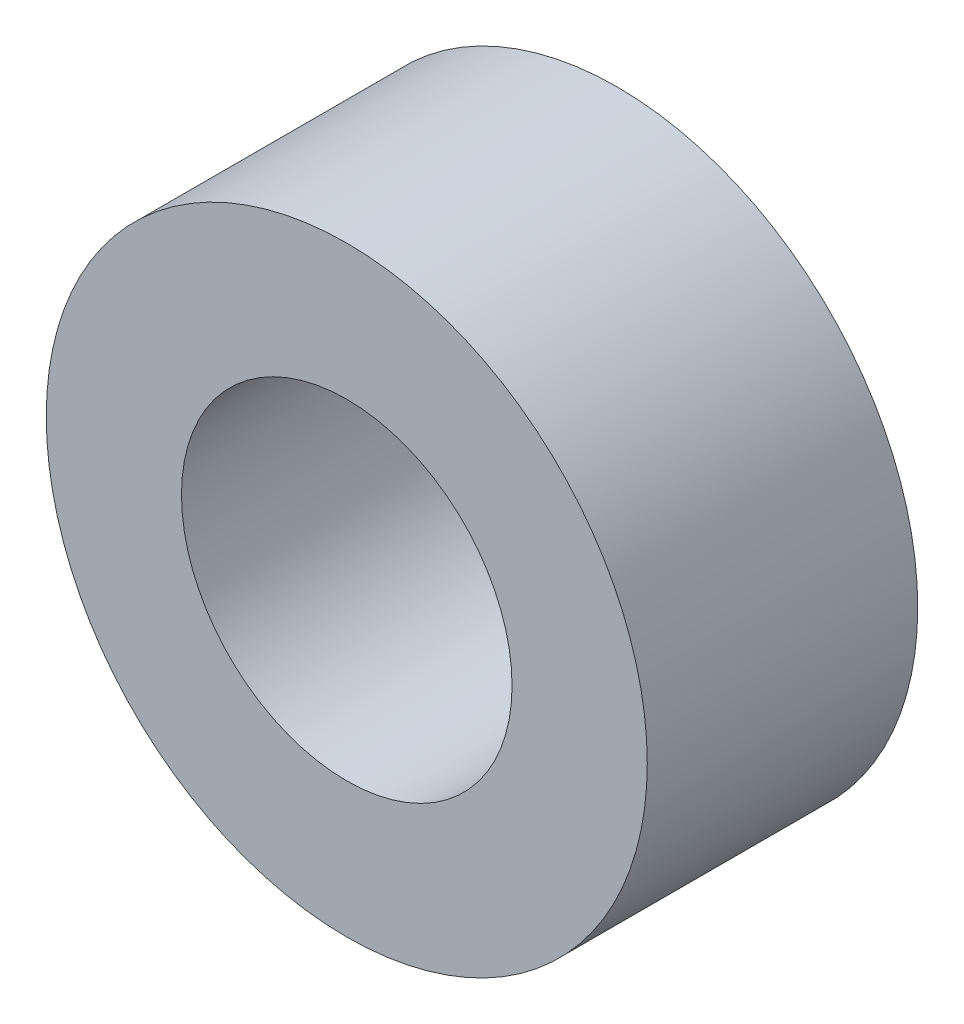
SolidWorks part; units mm, degrees
ref_plane "Piano frontale" through (0, 0, 0) normal (0, 0, 1) x (1, 0, 0)
ref_plane "Piano superiore" through (0, 0, 0) normal (0, 1, 0) x (1, 0, 0)
ref_plane "Piano destro" through (0, 0, 0) normal (1, 0, 0) x (0, 0, -1)
sketch "Schizzo1" plane through (0, 0, 0) normal (0, 0, 1) x (1, 0, 0)
  circle A0 centre (0, 0) radius 5
  dimension "D1" = 10
extrude "Estrusione-Estrusione1" add sketch "Schizzo1" along normal blind 4.5
sketch "Schizzo3" plane through (0, 0, 4.5) normal (0, 0, 1) x (1, 0, 0)
  line L0 (0, 5) -> (0, -5)
  line L1 (-5, 0) -> (5, 0)
  circle A0 centre (0, 0) radius 5 construction
  circle A1 centre (0, 0) radius 2.75
  dimension "D1" = 5.5
extrude "Taglio-Estrusione1" cut sketch "Schizzo3" against normal up to next contours A1
